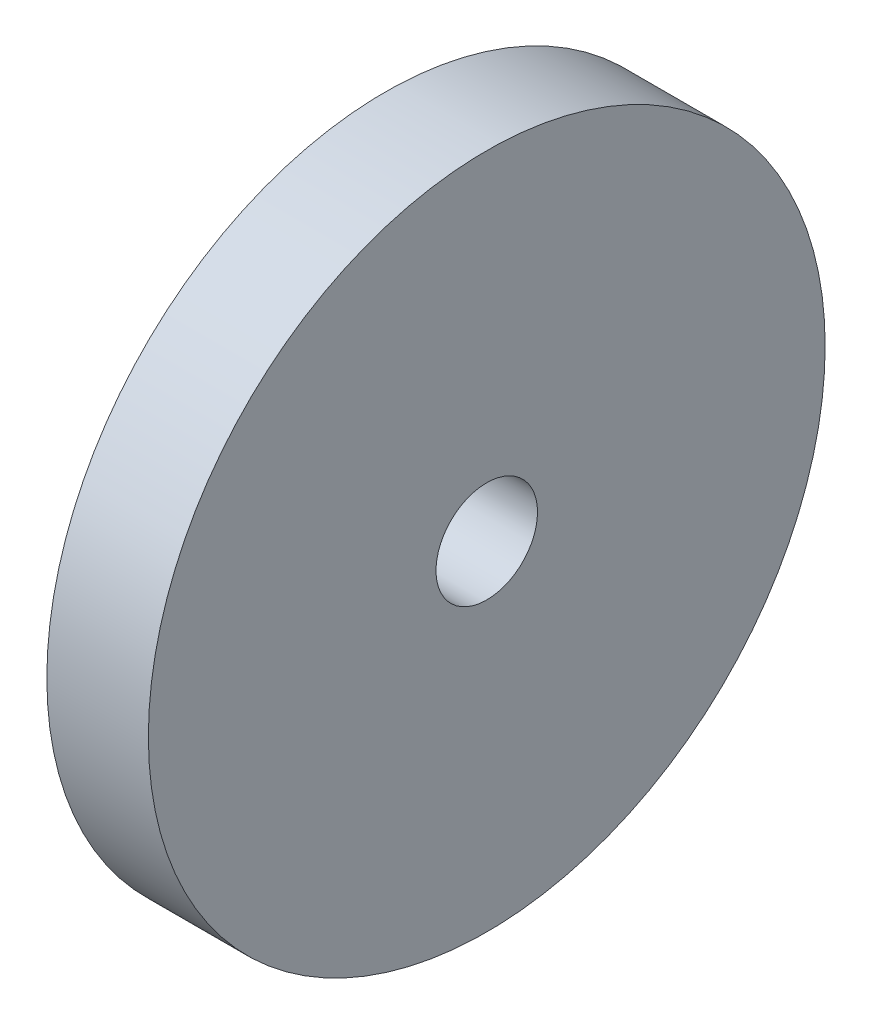
SolidWorks part; units mm, degrees
material "Pine"
ref_plane "Front Plane" through (0, 0, 0) normal (0, 0, 1) x (1, 0, 0)
ref_plane "Top Plane" through (0, 0, 0) normal (0, 1, 0) x (1, 0, 0)
ref_plane "Right Plane" through (0, 0, 0) normal (1, 0, 0) x (0, 0, -1)
sketch "Sketch1" plane through (0, 0, 0) normal (1, 0, 0) x (0, 0, -1)
  circle A0 centre (0, 0) radius 10
extrude "Boss-Extrude1" add sketch "Sketch1" along normal blind 3
sketch "Sketch2" plane through (3, 0, 0) normal (1, 0, 0) x (0, 0, -1)
  circle A0 centre (0, 0) radius 1.5
extrude "Cut-Extrude1" cut sketch "Sketch2" against normal through all
